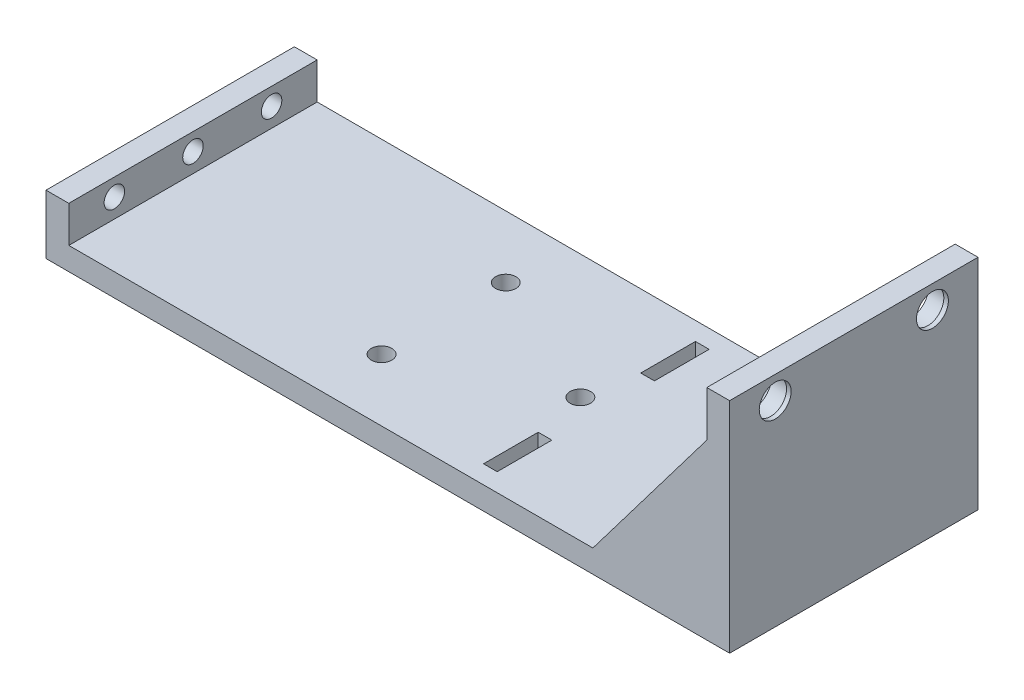
SolidWorks part; units mm, degrees
ref_plane "Front Plane" through (0, 0, 0) normal (0, 0, 1) x (1, 0, 0)
ref_plane "Top Plane" through (0, 0, 0) normal (0, 1, 0) x (1, 0, 0)
ref_plane "Right Plane" through (0, 0, 0) normal (1, 0, 0) x (0, 0, -1)
sketch "Sketch1" plane through (0, 0, 0) normal (0, 1, 0) x (1, 0, 0)
  line L2 (56.8875, -28.9394) -> (-93.1125, -28.9394)
  line L3 (56.8875, -28.9394) -> (56.8875, 25.5606)
  line L4 (56.8875, 25.5606) -> (-93.1125, 25.5606)
  line L5 (-93.1125, -28.9394) -> (-93.1125, 25.5606)
  dimension "D1" = 150
  dimension "D2" = 54.5
extrude "Boss-Extrude1" add sketch "Sketch1" along normal blind 5
sketch "Sketch2" plane through (0, 5, 0) normal (0, 1, 0) x (1, 0, 0)
  line L0 (-93.1125, -28.9394) -> (56.8875, -28.9394) construction
  line L1 (-93.1125, 25.5606) -> (-88.1125, 25.5606)
  line L2 (-93.1125, 25.5606) -> (-93.1125, -28.9394)
  line L3 (-93.1125, -28.9394) -> (-88.1125, -28.9394)
  line L4 (-88.1125, 25.5606) -> (-88.1125, -28.9394)
  dimension "D1" = 5
extrude "Boss-Extrude2" add sketch "Sketch2" along normal blind 8
hole_wizard "#8 Clearance Hole1" positions "3DSketch1" profile "Sketch3" hole size "#8" standard "ANSI Inch"
sketch3d "3DSketch1"
  line L1 (-93.1125, 13, -25.5606) -> (-93.1125, 13, 28.9394) construction
  line L2 (-93.1125, 13, -25.5606) -> (-93.1125, 0, -25.5606) construction
  line L3 (-93.1125, 13, 28.9394) -> (-93.1125, 0, 28.9394) construction
  point P0 (-93.1125, 9.2, -15.5606)
  point P2 (-93.1125, 9.2, 1.6894)
  point P4 (-93.1125, 9.2, 18.9394)
  dimension "D1" = 3.8
  dimension "D2" = 3.8
  dimension "D3" = 3.8
  dimension "D4" = 10
  dimension "D5" = 27.25
  dimension "D6" = 10
sketch "Sketch3" plane through (-93.1125, 9.2, -15.5606) normal (0, 1, 0) x (0, 0, 1)
  line L0 (0, 0) -> (0, 18.3507)
  line L1 (0, 18.3507) -> (2.2479, 17)
  line L2 (2.2479, 17) -> (2.2479, 0)
  line L5 (2.2479, 0) -> (0, 0)
  line L10 (0, 18.3507) -> (-2.2479, 17) construction
  line L11 (0, -6.35) -> (0, 107.95) construction
  dimension "Hole Dia." = 4.4958
  dimension "Hole Depth" = 17
  dimension "Drill Angle" = 118
sketch "Sketch7" plane through (0, 5, 0) normal (0, 1, 0) x (1, 0, 0)
  line L0 (56.8875, 25.5606) -> (-88.1125, 25.5606) construction
  line L1 (56.8875, -28.9394) -> (51.8875, -28.9394)
  line L2 (56.8875, -28.9394) -> (56.8875, 25.5606)
  line L3 (56.8875, 25.5606) -> (51.8875, 25.5606)
  line L4 (51.8875, -28.9394) -> (51.8875, 25.5606)
  dimension "D1" = 5
extrude "Boss-Extrude3" add sketch "Sketch7" along normal blind 43
sketch "Sketch8" plane through (51.8875, 0, 0) normal (-1, 0, 0) x (0, 0, 1)
  line L0 (-25.5606, 48) -> (28.9394, 48) construction
  line L1 (-25.5606, 48) -> (-25.5606, 5) construction
  line L2 (28.9394, 48) -> (28.9394, 5) construction
  circle A0 centre (-15.5606, 43) radius 4.25
  circle A1 centre (18.9394, 43) radius 4.25
  dimension "D1" = 8.5
  dimension "D2" = 8.5
  dimension "D3" = 5
  dimension "D4" = 5
  dimension "D5" = 10
  dimension "D6" = 10
extrude "Cut-Extrude1" cut sketch "Sketch8" against normal blind 4
sketch "Sketch10" plane through (0, 0, -25.5606) normal (0, 0, -1) x (-1, 0, 0)
  line L0 (-51.8875, 38) -> (-26.8875, 5)
  line L1 (-51.8875, 48) -> (-51.8875, 5) construction
  line L2 (-51.8875, 5) -> (88.1125, 5) construction
  dimension "D1" = 10
  dimension "D2" = 25
rib "Rib1" sketch "Sketch10" sketch "Sketch10" thickness 10 extrusion direction parallel to sketch draft on no parameters "D1"=10
sketch "Sketch12" plane through (0, 0, 28.9394) normal (0, 0, 1) x (1, 0, 0)
  line L0 (51.8875, 38) -> (26.8875, 5)
  line L1 (51.8875, 48) -> (51.8875, 5) construction
  line L2 (-88.1125, 5) -> (51.8875, 5) construction
  dimension "D1" = 10
  dimension "D2" = 25
rib "Rib3" sketch "Sketch12" sketch "Sketch12" thickness 10 extrusion direction parallel to sketch draft on no parameters "D1"=10
sketch "Sketch13" plane through (51.8875, 0, 0) normal (-1, 0, 0) x (0, 0, 1)
  line L0 (-25.5606, 48) -> (28.9394, 48) construction
  line L1 (-2.3106, 38) -> (5.6894, 38)
  line L2 (-2.3106, 38) -> (-2.3106, 36)
  line L3 (-2.3106, 36) -> (5.6894, 36)
  line L4 (5.6894, 38) -> (5.6894, 36)
  line L5 (-25.5606, 48) -> (-25.5606, 38) construction
  line L6 (28.9394, 48) -> (28.9394, 38) construction
  dimension "D1" = 8
  dimension "D2" = 10
  dimension "D3" = 23.25
  dimension "D4" = 23.25
  dimension "D5" = 2
extrude "Boss-Extrude4" add sketch "Sketch13" along normal blind 5
sketch "Sketch14" plane through (0, 38, 0) normal (0, 1, 0) x (1, 0, 0)
  line L0 (46.8875, -5.6894) -> (46.8875, 2.3106) construction
  line L1 (46.8875, 2.3106) -> (51.8875, 2.3106) construction
  circle A0 centre (49.3875, -1.6894) radius 2
  dimension "D1" = 2.5
  dimension "D2" = 4
extrude "Cut-Extrude2" cut sketch "Sketch14" against normal blind 2
sketch "Sketch15" plane through (55.8875, 0, 0) normal (-1, 0, 0) x (0, 0, 1)
  line L0 (28.9394, 48) -> (-25.5606, 48) construction
  circle A0 centre (-15.5606, 43) radius 3.5
  circle A1 centre (18.9394, 43) radius 3.5
  dimension "D1" = 5
  dimension "D2" = 5
extrude "Cut-Extrude3" cut sketch "Sketch15" against normal blind 1
sketch "Sketch16" plane through (0, 5, 0) normal (0, 1, 0) x (1, 0, 0)
  line L0 (56.8875, -28.9394) -> (56.8875, 25.5606) construction
  line L1 (1.8875, 21.5606) -> (-1.1125, 21.5606)
  line L2 (1.8875, 21.5606) -> (1.8875, 9.5606)
  line L3 (1.8875, 9.5606) -> (-1.1125, 9.5606)
  line L4 (-1.1125, 21.5606) -> (-1.1125, 9.5606)
  line L5 (26.8875, 25.5606) -> (-88.1125, 25.5606) construction
  line L6 (-88.1125, -28.9394) -> (26.8875, -28.9394) construction
  line L7 (1.8875, -12.9394) -> (-1.1125, -12.9394)
  line L8 (1.8875, -12.9394) -> (1.8875, -24.9394)
  line L9 (1.8875, -24.9394) -> (-1.1125, -24.9394)
  line L10 (-1.1125, -12.9394) -> (-1.1125, -24.9394)
  dimension "D1" = 55
  dimension "D2" = 12
  dimension "D3" = 3
  dimension "D4" = 4
  dimension "D5" = 12
  dimension "D6" = 4
  dimension "D7" = 55
  dimension "D8" = 3
extrude "Cut-Extrude4" cut sketch "Sketch16" against normal blind 5
hole_wizard "#8 Clearance Hole2" positions "3DSketch2" profile "Sketch17" hole size "#8" standard "ANSI Inch"
sketch3d "3DSketch2"
  line L1 (26.8875, 5, -25.5606) -> (-88.1125, 5, -25.5606) construction
  line L2 (-88.1125, 5, 28.9394) -> (26.8875, 5, 28.9394) construction
  line L5 (51.8875, 5, -15.5606) -> (51.8875, 5, 18.9394) construction
  point P0 (-3.1125, 5, 1.6894)
  point P2 (-33.1125, 5, 15.3144)
  point P4 (-33.1125, 5, -11.9356)
  dimension "D1" = 13.625
  dimension "D2" = 13.625
  dimension "D3" = 55
  dimension "D5" = 85
  dimension "D4" = 27.25
  dimension "D6" = 85
  dimension "D7" = 27.25
  dimension "D8" = 32.9491
  dimension "D9" = 32.9491
sketch "Sketch17" plane through (-3.1125, 5, 1.6894) normal (1, 0, 0) x (0, 0, 1)
  line L0 (0, 0) -> (0, 18.3507)
  line L1 (0, 18.3507) -> (2.2479, 17)
  line L2 (2.2479, 17) -> (2.2479, 0)
  line L5 (2.2479, 0) -> (0, 0)
  line L10 (0, 18.3507) -> (-2.2479, 17) construction
  line L11 (0, -6.35) -> (0, 107.95) construction
  dimension "Hole Dia." = 4.4958
  dimension "Hole Depth" = 17
  dimension "Drill Angle" = 118
